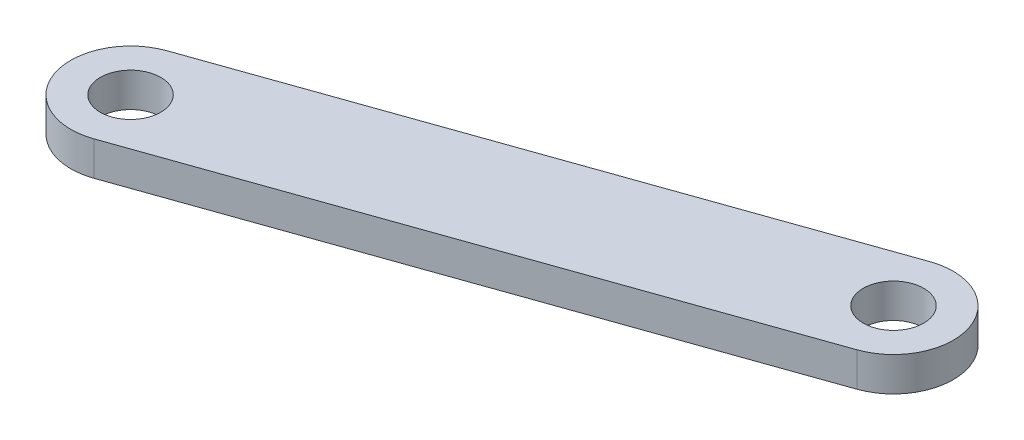
SolidWorks part; units mm, degrees
ref_plane "Front Plane" through (0, 0, 0) normal (0, 0, 1) x (1, 0, 0)
ref_plane "Top Plane" through (0, 0, 0) normal (0, 1, 0) x (1, 0, 0)
ref_plane "Right Plane" through (0, 0, 0) normal (1, 0, 0) x (0, 0, -1)
sketch "Sketch2" plane through (0, 0, 0) normal (0, 1, 0) x (1, 0, 0)
  line L0 (-65.3633, 0) -> (47.0746, 0) construction
  line L1 (5.989, 21.1607) -> (-5.0303, 27.4747) construction
  line L2 (-5.0303, 27.4747) -> (-46.953, 12.7) construction
  line L3 (-46.953, 12.7) -> (-46.953, -12.7) construction
  line L4 (-46.953, 0) -> (-78.4896, 0) construction
  line L5 (5.989, -21.1607) -> (-5.0303, -27.4747) construction
  line L6 (-5.0303, -27.4747) -> (-46.953, -12.7) construction
  line L7 (5.989, 21.1607) -> (5.9345, 21.0656) construction
  line L8 (5.989, -21.1607) -> (5.9345, -21.0656) construction
  line L9 (-6.5077, 31.6669) -> (-48.4304, 16.8923)
  line L10 (-26.67, -2.7134) -> (-46.953, -2.7134)
  line L11 (-26.67, -2.7134) -> (-26.67, 2.7134)
  line L12 (-26.67, 2.7134) -> (-46.953, 2.7134)
  line L13 (-46.953, -2.7134) -> (-46.953, 2.7134)
  line L14 (-26.67, -2.7134) -> (-46.953, 2.7134) construction
  line L15 (-26.67, 2.7134) -> (-46.953, -2.7134) construction
  line L16 (-3.5528, 23.2824) -> (-45.4755, 8.5077)
  arc A0 (5.989, 21.1607) -> (54.1983, 37.1763) centre (39.0466, 2.2186) cw construction
  arc A1 (5.989, -21.1607) -> (54.1983, -37.1763) centre (39.0466, -2.2186) ccw construction
  circle A2 centre (8.89, 0) radius 6.35 construction
  circle A3 centre (15.24, 0) radius 12.7 construction
  arc A5 (-48.4304, 16.8923) -> (-45.4755, 8.5077) centre (-46.953, 12.7) ccw
  arc A6 (-6.5077, 31.6669) -> (-3.5528, 23.2824) centre (-5.0303, 27.4747) cw
  point P25 (-36.8115, 0)
  dimension "D1" = 38.1
  dimension "D7" = 25.4
  dimension "D8" = 12.7
  dimension "D2" = 12.7
  dimension "D3" = 44.45
  dimension "D4" = 50.8
  dimension "D5" = 90
  dimension "D6" = 25.4
  dimension "D9" = 4.445
  dimension "D10" = 4.445
extrude "Boss-Extrude1" add sketch "Sketch2" along normal mid plane 2.54 contours A6 L9 A5 L16
sketch "Sketch3" plane through (0, 1.27, 0) normal (0, 1, 0) x (1, 0, 0)
  circle A0 centre (-5.0303, 27.4747) radius 2.2479
  circle A1 centre (-46.953, 12.7) radius 2.2479
  dimension "D1" = 4.4958
extrude "Cut-Extrude1" cut sketch "Sketch3" against normal up to next
